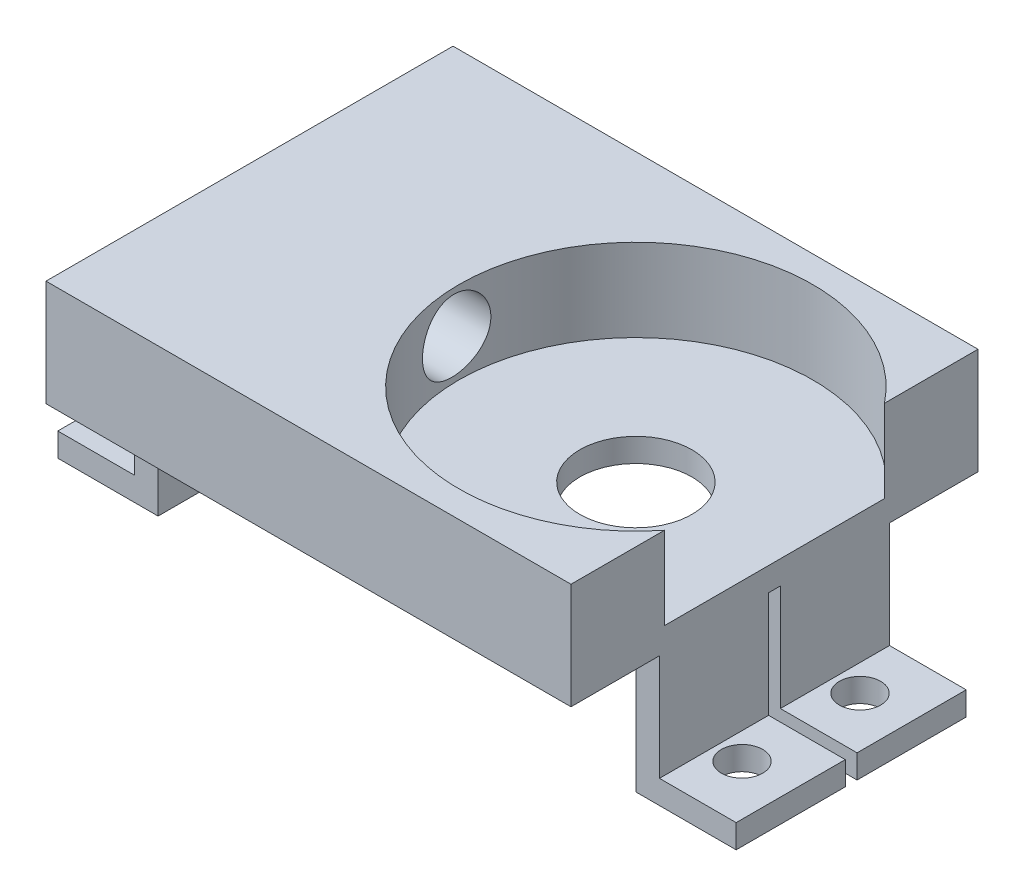
SolidWorks part; units mm, degrees
ref_plane "Front Plane" through (0, 0, 0) normal (0, 0, 1) x (1, 0, 0)
ref_plane "Top Plane" through (0, 0, 0) normal (0, 1, 0) x (1, 0, 0)
ref_plane "Right Plane" through (0, 0, 0) normal (1, 0, 0) x (0, 0, -1)
sketch "Sketch1" plane through (0, 0, 0) normal (0, 0, 1) x (1, 0, 0)
  line L0 (-9.0568, 11) -> (31.4432, 11)
  line L1 (31.4432, 11) -> (31.4432, 0)
  line L2 (31.4432, 0) -> (39.9432, 0)
  line L3 (39.9432, 0) -> (39.9432, 2)
  line L4 (39.9432, 2) -> (33.4432, 2)
  line L5 (33.4432, 2) -> (33.4432, 20)
  line L6 (33.4432, 20) -> (-11.0568, 20)
  line L7 (-11.0568, 20) -> (-11.0568, 2)
  line L8 (-11.0568, 2) -> (-17.5568, 2)
  line L9 (-17.5568, 2) -> (-17.5568, 0)
  line L10 (-17.5568, 0) -> (-9.0568, 0)
  line L11 (-9.0568, 0) -> (-9.0568, 11)
  dimension "D1" = 11
  dimension "D2" = 40.5
  dimension "D3" = 2
  dimension "D4" = 2
  dimension "D5" = 9
  dimension "D6" = 2
  dimension "D7" = 2
  dimension "D8" = 6.5
  dimension "D9" = 6.5
extrude "Boss-Extrude1" add sketch "Sketch1" along normal blind 34.5
sketch "Sketch3" plane through (0, 20, 0) normal (0, 1, 0) x (1, 0, 0)
  line L1 (33.4432, 0) -> (-11.0568, 0) construction
  line L2 (31.4432, -34.5) -> (31.4432, 0) construction
  circle A0 centre (21.6932, -17.25) radius 15
  dimension "D1" = 30
  dimension "D2" = 9.75
  dimension "D3" = 17.25
extrude "Cut-Extrude1" cut sketch "Sketch3" against normal blind 7
sketch "Sketch4" plane through (-17.5568, 0, 0) normal (-1, 0, 0) x (0, 0, 1)
  line L1 (0, 0) -> (7.5, 0)
  line L2 (0, 0) -> (0, 11)
  line L3 (0, 11) -> (7.5, 11)
  line L4 (7.5, 0) -> (7.5, 11)
  line L5 (34.5, 0) -> (27, 0)
  line L6 (34.5, 0) -> (34.5, 11)
  line L7 (34.5, 11) -> (27, 11)
  line L8 (27, 0) -> (27, 11)
  dimension "D1" = 7.5
  dimension "D2" = 7.5
  dimension "D3" = 11
  dimension "D4" = 11
extrude "Cut-Extrude2" cut sketch "Sketch4" against normal through all
sketch "Sketch5" plane through (0, 13, 0) normal (0, 1, 0) x (1, 0, 0)
  circle A0 centre (21.6932, -17.25) radius 4.75
  dimension "D1" = 9.5
extrude "Cut-Extrude3" cut sketch "Sketch5" against normal through all
sketch "Sketch6" plane through (39.9432, 0, 0) normal (1, 0, 0) x (0, 0, -1)
  line L0 (-27, 0) -> (-7.5, 0) construction
  line L1 (-17.75, 0) -> (-16.75, 0)
  line L2 (-17.75, 0) -> (-17.75, 11)
  line L3 (-17.75, 11) -> (-16.75, 11)
  line L4 (-16.75, 0) -> (-16.75, 11)
  line L5 (-7.5, 11) -> (0, 11) construction
  line L6 (-7.5, 2) -> (-7.5, 11) construction
  dimension "D1" = 1
  dimension "D2" = 0
  dimension "D3" = 9.25
extrude "Cut-Extrude4" cut sketch "Sketch6" against normal through all
sketch "Sketch7" plane through (-11.0568, 0, 0) normal (-1, 0, 0) x (0, 0, 1)
  line L0 (27, 2) -> (27, 11) construction
  line L1 (34.5, 20) -> (0, 20) construction
  circle A0 centre (17.75, 16.5) radius 3
  dimension "D1" = 6
  dimension "D2" = 9.25
  dimension "D3" = 3.5
extrude "Cut-Extrude5" cut sketch "Sketch7" against normal up to next
sketch "Sketch8" plane through (0, 2, 0) normal (0, 1, 0) x (1, 0, 0)
  line L0 (-11.0568, -7.5) -> (-17.5568, -7.5) construction
  line L1 (-17.5568, -16.75) -> (-17.5568, -7.5) construction
  line L2 (-17.5568, -27) -> (-17.5568, -17.75) construction
  line L3 (-17.5568, -27) -> (-11.0568, -27) construction
  line L4 (33.4432, -27) -> (39.9432, -27) construction
  line L5 (39.9432, -27) -> (39.9432, -17.75) construction
  line L6 (39.9432, -7.5) -> (33.4432, -7.5) construction
  line L7 (39.9432, -16.75) -> (39.9432, -7.5) construction
  circle A0 centre (-13.3068, -12.25) radius 1.75
  circle A1 centre (-13.3068, -22.25) radius 1.75
  circle A2 centre (35.6932, -22.25) radius 1.75
  circle A3 centre (35.6932, -12.25) radius 1.75
  dimension "D1" = 3.5
  dimension "D4" = 3.5
  dimension "D7" = 3.5
  dimension "D8" = 4.75
  dimension "D10" = 3.5
  dimension "D2" = 4.75
  dimension "D3" = 4.25
  dimension "D5" = 4.25
  dimension "D6" = 4.75
  dimension "D9" = 4.25
  dimension "D11" = 4.75
  dimension "D12" = 4.25
extrude "Cut-Extrude6" cut sketch "Sketch8" against normal through all
